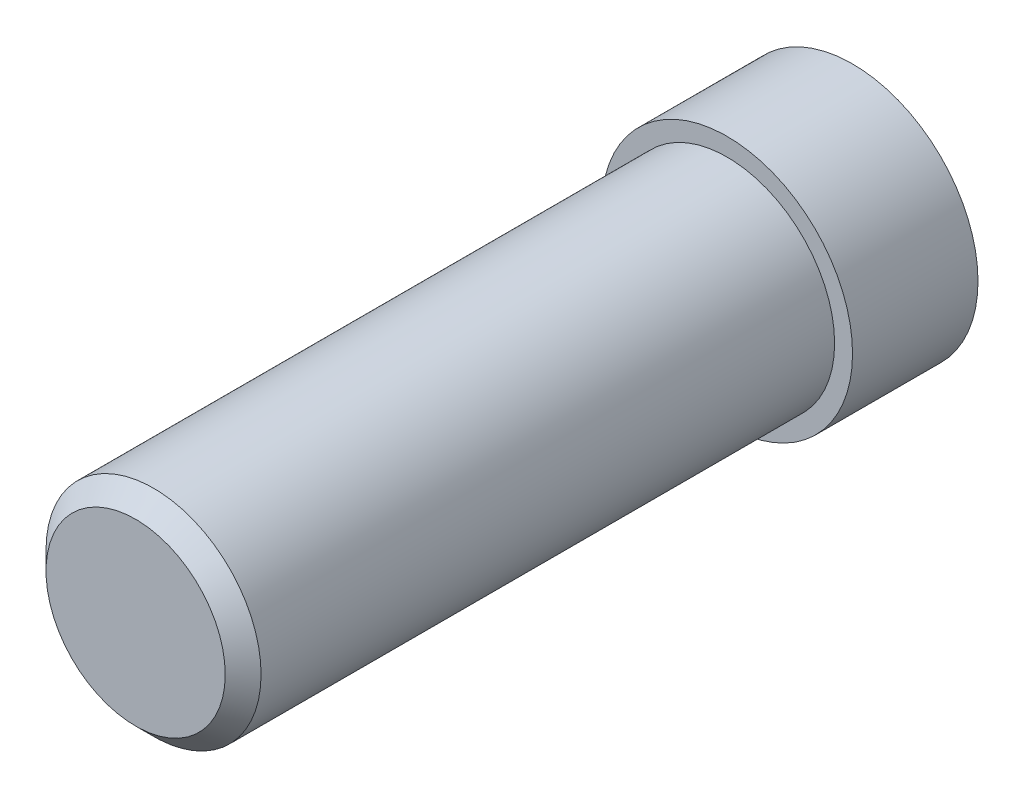
SolidWorks part; units mm, degrees
ref_plane "Front" through (0, 0, 0) normal (0, 0, 1) x (1, 0, 0)
ref_plane "Top" through (0, 0, 0) normal (0, 1, 0) x (1, 0, 0)
ref_plane "Right" through (0, 0, 0) normal (1, 0, 0) x (0, 0, -1)
sketch "Sketch1" plane through (0, 0, 0) normal (0, 0, 1) x (1, 0, 0)
  circle A0 centre (0, 0) radius 7
  dimension "D1" = 14
extrude "Boss-Extrude1" add sketch "Sketch1" along normal blind 7 contours A0
sketch "Sketch2" plane through (0, 0, 7) normal (0, 0, 1) x (1, 0, 0)
  circle A0 centre (0, 0) radius 6
  dimension "D1" = 12
extrude "Boss-Extrude2" add sketch "Sketch2" along normal blind 33
chamfer "Chamfer1" distance 1 angle 45 1 edges at (6, 0, 40)
